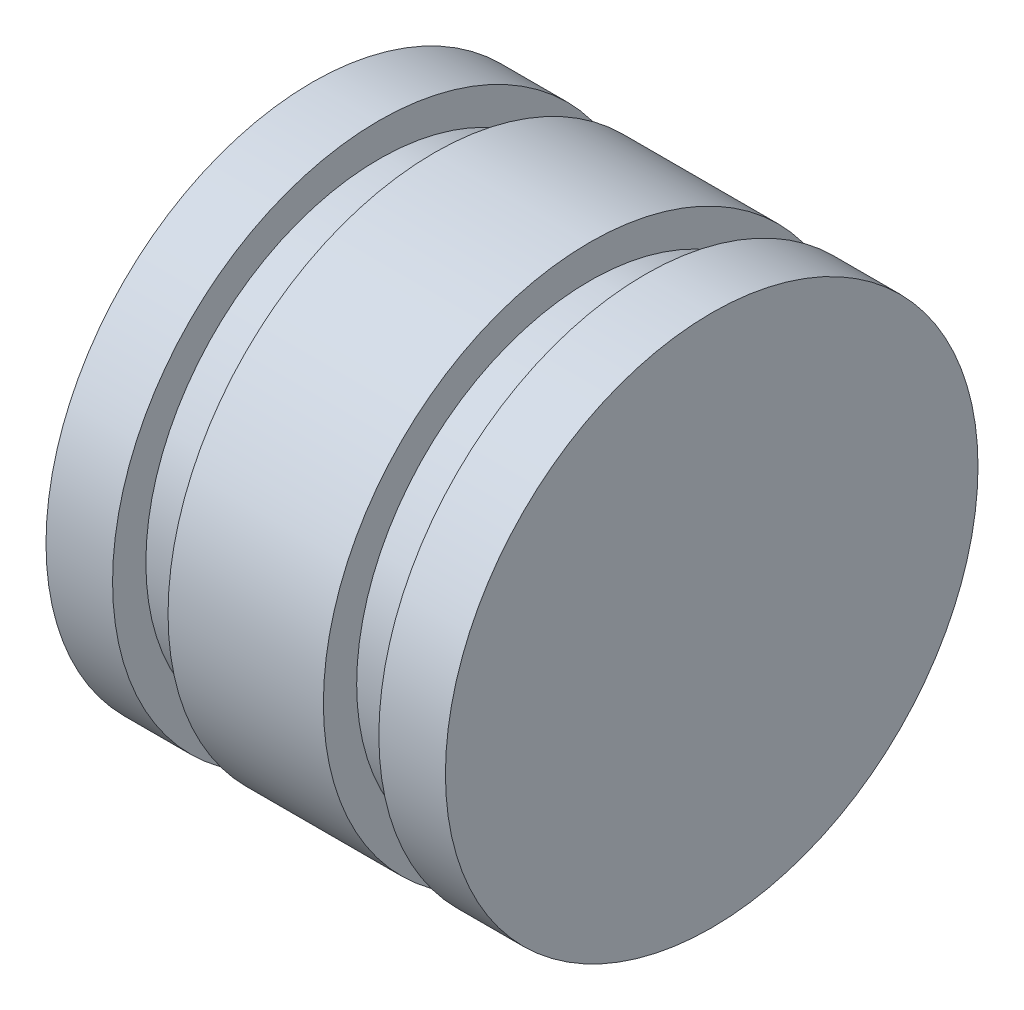
SolidWorks part; units mm, degrees
ref_plane "Front Plane" through (0, 0, 0) normal (0, 0, 1) x (1, 0, 0)
ref_plane "Top Plane" through (0, 0, 0) normal (0, 1, 0) x (1, 0, 0)
ref_plane "Right Plane" through (0, 0, 0) normal (1, 0, 0) x (0, 0, -1)
sketch "Sketch1" plane through (0, 0, 0) normal (0, 1, 0) x (1, 0, 0)
  line L0 (-18.3193, -5.6061) -> (-18.3193, -4.1061)
  line L1 (-21.3193, 6.3939) -> (-3.3193, 6.3939)
  line L2 (-21.3193, 6.3939) -> (-21.3193, -5.6061)
  line L3 (-21.3193, -5.6061) -> (-18.3193, -5.6061)
  line L4 (-3.3193, 6.3939) -> (-3.3193, -5.6061)
  line L5 (-21.3193, 6.3939) -> (-3.3193, -5.6061) construction
  line L6 (-21.3193, -5.6061) -> (-3.3193, 6.3939) construction
  line L7 (-18.3193, -4.1061) -> (-15.8193, -4.1061)
  line L8 (-15.8193, -4.1061) -> (-15.8193, -5.6061)
  line L9 (-8.8193, -5.6061) -> (-8.8193, -4.1061)
  line L10 (-8.8193, -4.1061) -> (-6.3193, -4.1061)
  line L11 (-6.3193, -4.1061) -> (-6.3193, -5.6061)
  line L12 (-15.8193, -5.6061) -> (-8.8193, -5.6061)
  line L13 (-6.3193, -5.6061) -> (-3.3193, -5.6061)
  line L14 (-21.3193, 6.3939) -> (1.3406, 6.3939) construction
  point P0 (-12.3193, 0.3939)
  dimension "D1" = 12
  dimension "D2" = 7
  dimension "D3" = 1.5
  dimension "D4" = 1.5
  dimension "D5" = 2.5
  dimension "D6" = 2.5
  dimension "D7" = 3
  dimension "D8" = 3
revolve "Revolve1" add sketch "Sketch1" angle 360 about L1
